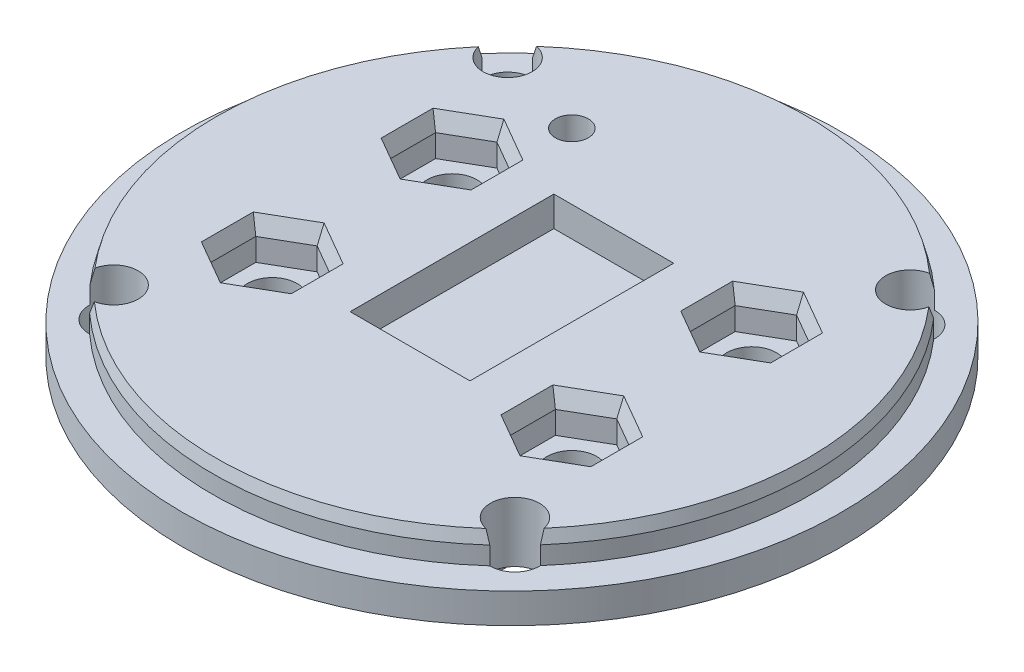
SolidWorks part; units mm, degrees
ref_plane "Спереди" through (0, 0, 0) normal (0, 0, 1) x (1, 0, 0)
ref_plane "Сверху" through (0, 0, 0) normal (0, 1, 0) x (1, 0, 0)
ref_plane "Справа" through (0, 0, 0) normal (1, 0, 0) x (0, 0, -1)
sketch "Эскиз1" plane through (0, 0, 0) normal (0, 1, 0) x (1, 0, 0)
  circle A0 centre (0, 0) radius 55
  dimension "D1" = 110
extrude "Бобышка-Вытянуть1" add sketch "Эскиз1" along normal blind 5
sketch "Эскиз2" plane through (0, 5, 0) normal (0, 1, 0) x (1, 0, 0)
  circle A0 centre (0, 0) radius 49.9
  dimension "D1" = 99.8
extrude "Бобышка-Вытянуть2" add sketch "Эскиз2" along normal blind 5
sketch "Эскиз3" plane through (0, 0, 0) normal (0, -1, 0) x (1, 0, 0)
  line L1 (17.5, -22.5) -> (-17.5, -22.5)
  line L2 (17.5, -22.5) -> (17.5, 22.5)
  line L3 (17.5, 22.5) -> (-17.5, 22.5)
  line L4 (-17.5, -22.5) -> (-17.5, 22.5)
  line L5 (17.5, -22.5) -> (-17.5, 22.5) construction
  line L6 (17.5, 22.5) -> (-17.5, -22.5) construction
  point P0 (0, 0)
  dimension "D1" = 35
  dimension "D2" = 45
extrude "Бобышка-Вытянуть3" add sketch "Эскиз3" along normal blind 25
sketch "Эскиз4" plane through (0, 0, 22.5) normal (0, 0, 1) x (1, 0, 0)
  line L0 (-17.5, 0) -> (17.5, -25) construction
  line L2 (10.1, -17.65) -> (-10.1, -17.65)
  line L3 (10.1, -17.65) -> (10.1, -7.35)
  line L4 (10.1, -7.35) -> (-10.1, -7.35)
  line L5 (-10.1, -17.65) -> (-10.1, -7.35)
  line L6 (10.1, -17.65) -> (-10.1, -7.35) construction
  line L7 (10.1, -7.35) -> (-10.1, -17.65) construction
  point P4 (0, -12.5)
  dimension "D1" = 20.2
  dimension "D2" = 10.3
extrude "Вырез-Вытянуть1" cut sketch "Эскиз4" against normal through all
sketch "Эскиз5" plane through (0, 0, 0) normal (0, -1, 0) x (1, 0, 0)
  line L0 (23.35, -22.85) -> (39.3102, -38.467) construction
  line L5 (-23.35, 22.85) -> (23.35, -22.85) construction
  line L6 (-23.35, -22.85) -> (23.35, 22.85) construction
  line L7 (-23.35, 22.85) -> (-39.3095, 38.4677) construction
  line L8 (23.35, 22.85) -> (39.1401, 38.6401) construction
  line L9 (-23.35, -22.85) -> (-39.3095, -38.4677) construction
  circle A0 centre (0, 0) radius 55 construction
  circle A1 centre (33.5922, -32.8719) radius 4.1
  circle A2 centre (-33.5917, -32.8724) radius 4.1
  circle A3 centre (-33.5917, 32.8724) radius 4.1
  circle A4 centre (33.4832, 32.9832) radius 4.1
  point P0 (0, 0)
  dimension "D3" = 8.2
  dimension "D1" = 46.7
  dimension "D2" = 45.7
  dimension "D4" = 8
  dimension "D5" = 8
  dimension "D6" = 8
  dimension "D7" = 8
extrude "Вырез-Вытянуть2" cut sketch "Эскиз5" against normal through all
sketch "Эскиз6" plane through (0, 10, 0) normal (0, 1, 0) x (1, 0, 0)
  line L0 (0, 0) -> (0.0004, 49.9) construction
  line L1 (0.0002, 28) -> (-17.9998, 28) construction
  arc A0 (33.5133, 36.9712) -> (-33.5128, 36.9717) centre (0, 0) ccw construction
  circle A1 centre (-17.9998, 28) radius 2.75
  dimension "D3" = 5.5
  dimension "D1" = 28
  dimension "D2" = 18
extrude "Вырез-Вытянуть3" cut sketch "Эскиз6" against normal through all
chamfer "Chamfer1" distance 2 angle 15 4 edges at (-0.0824, 10, 49.8999) (-49.9, 10, 0) (0.0004, 10, -49.9) (49.8999, 10, 0.0826)
sketch "Sketch2" plane through (0, -25, 0) normal (0, -1, 0) x (1, 0, 0)
  line L0 (17.5, 0) -> (-17.5652, 0) construction
  line L1 (17.5, -22.5) -> (17.5, 22.5) construction
  line L4 (-17.5652, -22.5) -> (17.5, -22.5)
  line L5 (-17.5652, -22.5) -> (-17.5652, 22.5)
  line L6 (-17.5652, 22.5) -> (17.5, 22.5)
  line L7 (17.5, -22.5) -> (17.5, 22.5)
  line L8 (-17.5652, -22.5) -> (17.5, 22.5) construction
  line L9 (-17.5652, 22.5) -> (17.5, -22.5) construction
  point P6 (-0.0326, 0)
extrude "Cut-Extrude1" cut sketch "Sketch2" against normal blind 12.5
sketch "Sketch4" plane through (0, -7.35, 0) normal (0, -1, 0) x (1, 0, 0)
  line L1 (-35, -22.5) -> (35, -22.5)
  line L2 (-35, -22.5) -> (-35, 22.5)
  line L3 (-35, 22.5) -> (35, 22.5)
  line L4 (35, -22.5) -> (35, 22.5)
  line L5 (-35, -22.5) -> (35, 22.5) construction
  line L6 (-35, 22.5) -> (35, -22.5) construction
  point P0 (0, 0)
  dimension "D1" = 45
  dimension "D2" = 70
extrude "Boss-Extrude1" add sketch "Sketch4" against normal up to surface (5.35 mm away) from offset 2 up to face at (-17.9998, 0, -25.25) offset against normal yes
sketch "Sketch5" plane through (0, -5.35, 0) normal (0, -1, 0) x (1, 0, 0)
  line L0 (25, 22.5) -> (25, -22.5) construction
  line L1 (35, 22.5) -> (17.5, 22.5) construction
  line L2 (17.5, -22.5) -> (35, -22.5) construction
  line L3 (-25, 22.5) -> (-25, -22.5) construction
  line L4 (-17.5, 22.5) -> (-35, 22.5) construction
  line L5 (-35, -22.5) -> (-17.5, -22.5) construction
  line L6 (25, 15) -> (-25, 15) construction
  line L7 (25, -15) -> (-25, -15) construction
  circle A0 centre (25, 15) radius 4.15
  circle A1 centre (-25, 15) radius 4.15
  circle A2 centre (25, -15) radius 4.15
  circle A3 centre (-25, -15) radius 4.15
  point P21 (25, 0)
  dimension "D1" = 8.3
  dimension "D2" = 50
  dimension "D3" = 25
  dimension "D4" = 30
  dimension "D5" = 15
extrude "Cut-Extrude2" cut sketch "Sketch5" against normal through all
sketch "Sketch6" plane through (0, 10, 0) normal (0, 1, 0) x (1, 0, 0)
  line L1 (-18.5048, -11.25) -> (-25, -7.5)
  line L2 (-25, -7.5) -> (-31.4952, -11.25)
  line L3 (-31.4952, -11.25) -> (-31.4952, -18.75)
  line L4 (-31.4952, -18.75) -> (-25, -22.5)
  line L5 (-25, -22.5) -> (-18.5048, -18.75)
  line L6 (-18.5048, -18.75) -> (-18.5048, -11.25)
  line L7 (31.4952, -11.25) -> (25, -7.5)
  line L8 (25, -7.5) -> (18.5048, -11.25)
  line L9 (18.5048, -11.25) -> (18.5048, -18.75)
  line L10 (18.5048, -18.75) -> (25, -22.5)
  line L11 (25, -22.5) -> (31.4952, -18.75)
  line L12 (31.4952, -18.75) -> (31.4952, -11.25)
  line L13 (31.4952, 18.75) -> (25, 22.5)
  line L14 (25, 22.5) -> (18.5048, 18.75)
  line L15 (18.5048, 18.75) -> (18.5048, 11.25)
  line L16 (18.5048, 11.25) -> (25, 7.5)
  line L17 (25, 7.5) -> (31.4952, 11.25)
  line L18 (31.4952, 11.25) -> (31.4952, 18.75)
  line L19 (-18.5048, 18.75) -> (-25, 22.5)
  line L20 (-25, 22.5) -> (-31.4952, 18.75)
  line L21 (-31.4952, 18.75) -> (-31.4952, 11.25)
  line L22 (-31.4952, 11.25) -> (-25, 7.5)
  line L23 (-25, 7.5) -> (-18.5048, 11.25)
  line L24 (-18.5048, 11.25) -> (-18.5048, 18.75)
  circle A0 centre (-25, -15) radius 7.5 construction
  circle A1 centre (25, -15) radius 7.5 construction
  circle A2 centre (25, 15) radius 7.5 construction
  circle A3 centre (-25, 15) radius 7.5 construction
  dimension "D1" = 15
extrude "Cut-Extrude3" cut sketch "Sketch6" against normal blind 6.5
sketch "Sketch7" plane through (0, 10, 0) normal (0, 1, 0) x (1, 0, 0)
  line L1 (-10, -17) -> (10, -17)
  line L2 (-10, -17) -> (-10, 17)
  line L3 (-10, 17) -> (10, 17)
  line L4 (10, -17) -> (10, 17)
  line L5 (-10, -17) -> (10, 17) construction
  line L6 (-10, 17) -> (10, -17) construction
  point P0 (0, 0)
  dimension "D1" = 20
  dimension "D2" = 34
extrude "Cut-Extrude4" cut sketch "Sketch7" against normal blind 5
chamfer "Chamfer2" distance 1 angle 70 24 edges at (-28.2476, 10, 9.375) (-31.4952, 10, 15) (-28.2476, 10, 20.625) (-21.7524, 10, 20.625) (-18.5048, 10, 15) (-21.7524, 10, 9.375) (18.5048, 10, 15) (21.7524, 10, 20.625) (28.2476, 10, 20.625) (31.4952, 10, 15) (28.2476, 10, 9.375) (21.7524, 10, 9.375) (-28.2476, 10, -9.375) (-31.4952, 10, -15) (-28.2476, 10, -20.625) (-21.7524, 10, -20.625) (-18.5048, 10, -15) (-21.7524, 10, -9.375) (21.7524, 10, -9.375) (18.5048, 10, -15) (21.7524, 10, -20.625) (28.2476, 10, -20.625) (31.4952, 10, -15) (28.2476, 10, -9.375)
